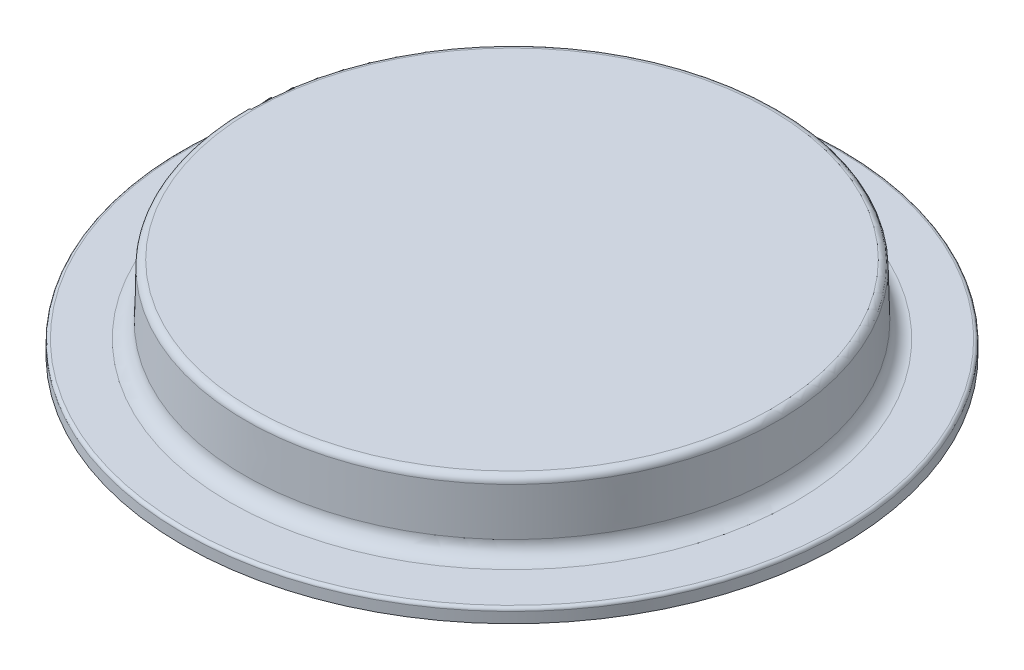
SolidWorks part; units mm, degrees
material "Rubber"
ref_plane "Front" through (0, 0, 0) normal (0, 0, 1) x (1, 0, 0)
ref_plane "Top" through (0, 0, 0) normal (0, 1, 0) x (1, 0, 0)
ref_plane "Right" through (0, 0, 0) normal (1, 0, 0) x (0, 0, -1)
sketch "Sketch1" plane through (0, 0, 0) normal (1, 0, 0) x (0, 0, -1)
  line L0 (-6.35, -0.7938) -> (6.35, -0.7938) construction
  line L1 (0, -0.7938) -> (0, 0.7938) construction
  point P7 (0, 0)
  dimension "OD" = 12.7
  dimension "Height" = 1.5875
sketch "Sketch2" plane through (0, 0, 0) normal (1, 0, 0) x (0, 0, -1)
  line L0 (-6.35, -0.7938) -> (-6.35, -0.5292)
  line L1 (-6.35, -0.5292) -> (-5.1556, -0.5292)
  line L2 (-5.1556, -0.5292) -> (-5.1244, 0.6639)
  line L3 (-4.9911, 0.7938) -> (0, 0.7938)
  line L4 (-6.35, -0.7938) -> (0, -0.7938)
  line L5 (0, 0.7938) -> (0, -0.7938)
  arc A0 (-4.9911, 0.7938) -> (-5.1244, 0.6639) centre (-4.9911, 0.6604) ccw
  dimension "D3" = 0.1334
  dimension "D1" = 0.2646
  dimension "D2" = 4.9911
  dimension "D4" = 1.5
  dimension "D5" = 1.1944
revolve "Revolve1" add sketch "Sketch2" angle 360 about L1
fillet "Fillet1" radius 0.2986 1 edges at (0, -0.5292, -5.1556)
fillet "Fillet2" radius 0.0597 1 edges at (0, -0.5292, -6.35)
sketch "Sketch3" plane through (0, 0, 0) normal (0, 0, 1) x (1, 0, 0)
  line L0 (-6.35, 0.7938) -> (-6.35, -0.7937) construction
  line L1 (0, -0.7938) -> (0, 0.7938) construction
